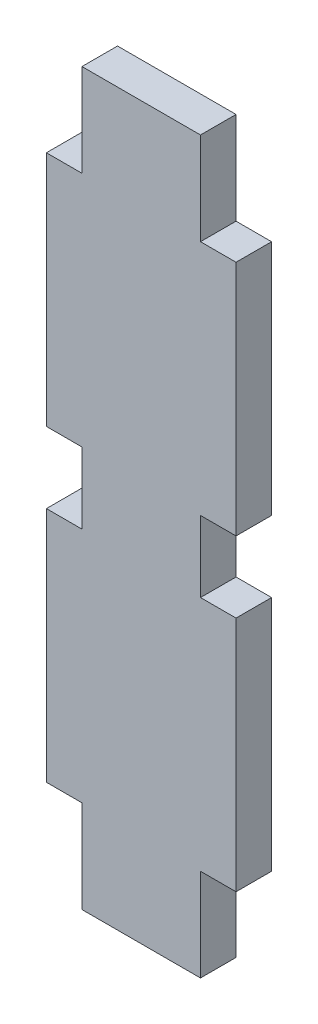
SolidWorks part; units mm, degrees
ref_plane "Front Plane" through (0, 0, 0) normal (0, 0, 1) x (1, 0, 0)
ref_plane "Top Plane" through (0, 0, 0) normal (0, 1, 0) x (1, 0, 0)
ref_plane "Right Plane" through (0, 0, 0) normal (1, 0, 0) x (0, 0, -1)
sketch "Sketch1" plane through (0, 0, 0) normal (0, 0, 1) x (1, 0, 0)
  line L0 (3, -428.2) -> (13, -428.2)
  line L3 (3, -428.2) -> (3, -436)
  line L4 (13, -482) -> (13, -489.8)
  line L7 (16, -482) -> (13, -482)
  line L8 (0, -436) -> (0, -456)
  line L9 (0, -456) -> (3, -456)
  line L11 (3, -436) -> (0, -436)
  line L14 (16, -462) -> (16, -482)
  line L17 (0, -482) -> (3, -482)
  line L19 (3, -462) -> (0, -462)
  line L21 (13, -462) -> (16, -462)
  line L22 (3, -456) -> (3, -462)
  line L23 (0, -462) -> (0, -482)
  line L24 (3, -482) -> (3, -489.8)
  line L25 (3, -489.8) -> (13, -489.8)
  line L26 (13, -428.2) -> (13, -436)
  line L27 (13, -456) -> (13, -462)
  line L28 (16, -456) -> (13, -456)
  line L29 (16, -436) -> (16, -456)
  line L30 (13, -436) -> (16, -436)
extrude "Boss-Extrude1" add sketch "Sketch1" along normal blind 3
